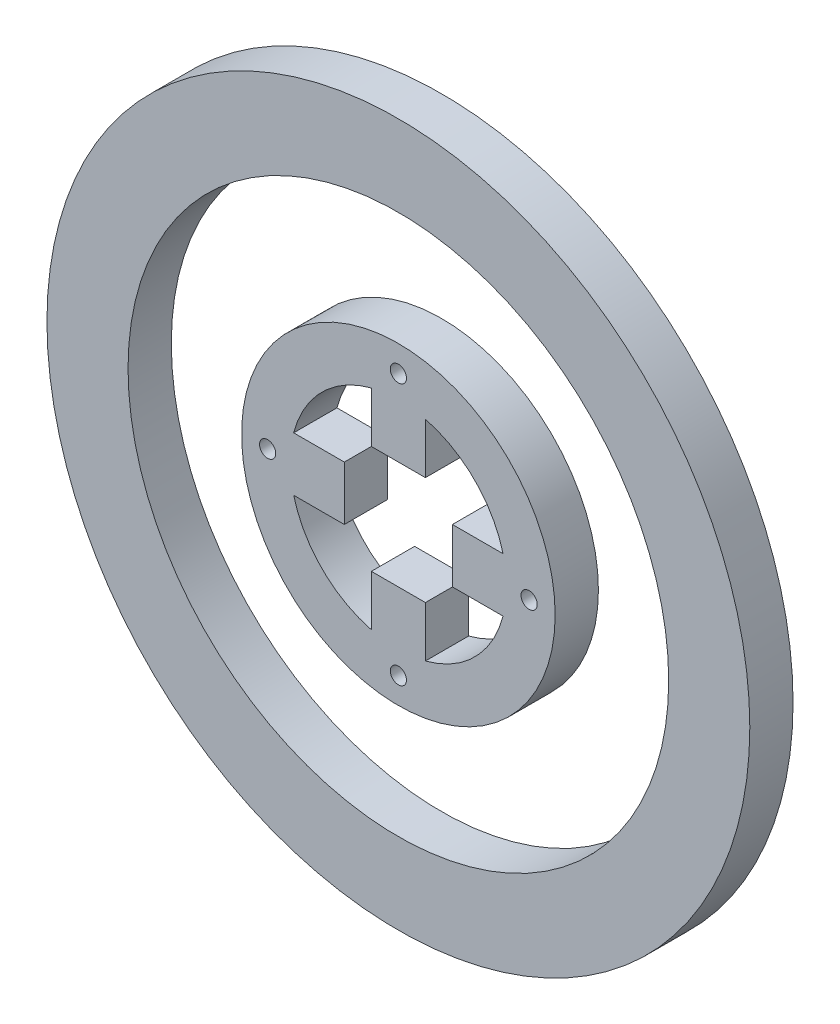
SolidWorks part; units mm, degrees
ref_plane "Front Plane" through (0, 0, 0) normal (0, 0, 1) x (1, 0, 0)
ref_plane "Top Plane" through (0, 0, 0) normal (0, 1, 0) x (1, 0, 0)
ref_plane "Right Plane" through (0, 0, 0) normal (1, 0, 0) x (0, 0, -1)
sketch "Sketch1" plane through (0, 0, 0) normal (0, 0, 1) x (1, 0, 0)
  circle A0 centre (0, 0) radius 65
  circle A1 centre (0, 0) radius 50
  dimension "D1" = 130
  dimension "D2" = 100
extrude "Outer Ring" add sketch "Sketch1" along normal blind 8
sketch "Sketch6" plane through (0, 0, 8) normal (0, 0, 1) x (1, 0, 0)
  circle A0 centre (0, 0) radius 20
  circle A1 centre (0, 0) radius 29
  dimension "D1" = 40
  dimension "D2" = 58
extrude "Inner Ring" add sketch "Sketch6" against normal blind 8 separate body
sketch "Sketch7" plane through (0, 0, 8) normal (0, 0, 1) x (1, 0, 0)
  line L2 (-10, 5) -> (-10, -5)
  line L3 (-5, 10) -> (5, 10)
  line L4 (10, 5) -> (10, -5)
  line L5 (-5, -10) -> (5, -10)
  line L14 (-19.3649, 5) -> (-10, 5)
  line L15 (-19.3649, -5) -> (-10, -5)
  line L16 (-5, 19.3649) -> (-5, 10)
  line L17 (5, 19.3649) -> (5, 10)
  line L18 (19.3649, 5) -> (10, 5)
  line L19 (19.3649, -5) -> (10, -5)
  line L20 (5, -19.3649) -> (5, -10)
  line L21 (-5, -19.3649) -> (-5, -10)
  circle A1 centre (0, 0) radius 20
  circle M19 centre (0, 0) radius 20
  dimension "D1" = 20
  dimension "D2" = 20
  dimension "D3" = 10
  dimension "D5" = 10
  dimension "D7" = 10
  dimension "D8" = 10
extrude "Motor Connector Cut" add sketch "Sketch7" against normal blind 8 contours L19 L18 L4 M19 | L17 L16 L3 M19 | L15 L2 L14 M19 | L21 L20 L5 M19
sketch "Sketch8" plane through (0, 0, 8) normal (0, 0, 1) x (1, 0, 0)
  circle A1 centre (0, 24.1825) radius 1.5
  circle A2 centre (24.1825, 0) radius 1.5
  circle A3 centre (0, -24.1825) radius 1.5
  circle A4 centre (-24.1825, 0) radius 1.5
  dimension "D1" = 3
  dimension "D2" = 3
  dimension "D3" = 3
  dimension "D4" = 3
  dimension "D6" = 48.3649
  dimension "D8" = 48.3649
extrude "M3 Holes" cut sketch "Sketch8" against normal blind 14 and the other way blind 38
